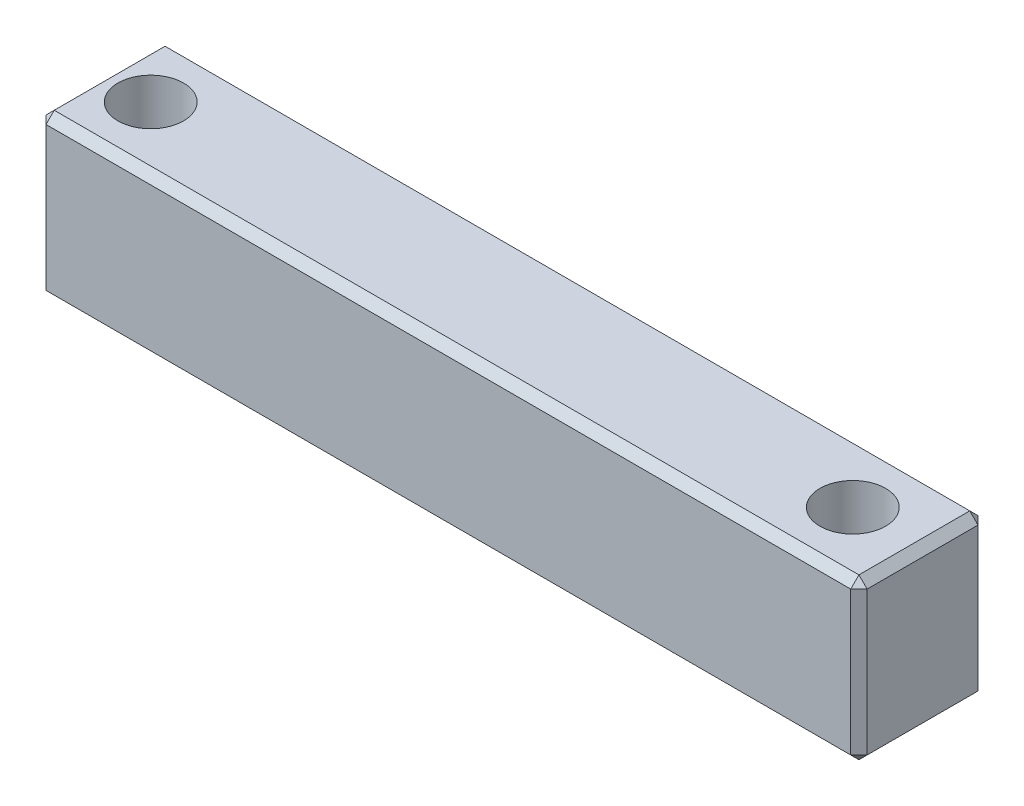
SolidWorks part; units mm, degrees
ref_plane "Front Plane" through (0, 0, 0) normal (0, 0, 1) x (1, 0, 0)
ref_plane "Top Plane" through (0, 0, 0) normal (0, 1, 0) x (1, 0, 0)
ref_plane "Right Plane" through (0, 0, 0) normal (1, 0, 0) x (0, 0, -1)
sketch "Sketch1" plane through (0, 0, 0) normal (1, 0, 0) x (0, 0, -1)
  line L1 (0, 0) -> (7.75, 0)
  line L2 (0, 0) -> (0, 9.75)
  line L3 (0, 9.75) -> (7.75, 9.75)
  line L4 (7.75, 0) -> (7.75, 9.75)
  dimension "D1" = 7.75
  dimension "D2" = 9.75
extrude "Boss-Extrude1" add sketch "Sketch1" along normal blind 50
sketch "Sketch4" plane through (0, 9.75, 0) normal (0, 1, 0) x (1, 0, 0)
  line L0 (0, 3.875) -> (3, 3.875) construction
  line L1 (0, 7.75) -> (0, 0) construction
  line L2 (50, 3.875) -> (45.75, 3.875) construction
  line L3 (50, 7.75) -> (50, 0) construction
  circle A2 centre (3, 3.875) radius 2
  circle A3 centre (45.75, 3.875) radius 2
  dimension "D2" = 4.25
  dimension "D1" = 3
extrude "Cut-Extrude3" cut sketch "Sketch4" against normal up to surface (9.75 mm away) up to face at (25, 0, -3.875)
chamfer "Chamfer1" distance 0.5 angle 45 12 edges at (50, 4.875, 0) (50, 9.75, -3.875) (25, 9.75, 0) (0, 9.75, -3.875) (0, 4.875, 0) (25, 0, 0) (50, 0, -3.875) (0, 0, -3.875) (25, 0, -7.75) (50, 4.875, -7.75) (25, 9.75, -7.75) (0, 4.875, -7.75)
